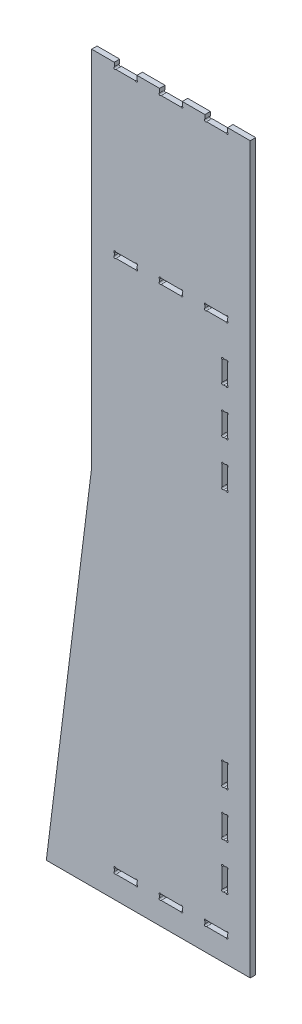
SolidWorks part; units mm, degrees
ref_plane "Front Plane" through (0, 0, 0) normal (0, 0, 1) x (1, 0, 0)
ref_plane "Top Plane" through (0, 0, 0) normal (0, 1, 0) x (1, 0, 0)
ref_plane "Right Plane" through (0, 0, 0) normal (1, 0, 0) x (0, 0, -1)
sketch "Sketch1" plane through (0, 0, 0) normal (0, 0, 1) x (1, 0, 0)
  line L0 (230.2639, 423.1047) -> (230.2639, -376.8953)
  line L1 (230.2639, -376.8953) -> (-219.7361, -376.8953)
  line L2 (-69.7361, 1218.1047) -> (-69.7361, 1214.3832)
  line L3 (-219.7361, -376.8953) -> (-119.7361, 423.1047)
  line L4 (230.2639, 423.1047) -> (230.2639, 1223.1047)
  line L5 (230.2639, 1223.1047) -> (180.2639, 1223.1047)
  line L6 (-119.7361, 1223.1047) -> (-119.7361, 423.1047)
  line L7 (-66.4577, 1211.1047) -> (-23.0146, 1211.1047)
  line L8 (-19.7361, 1214.3832) -> (-19.7361, 1218.1047)
  line L9 (-69.7361, 1223.1047) -> (-119.7361, 1223.1047)
  line L10 (30.2639, 1218.1047) -> (30.2639, 1214.3832)
  line L11 (33.5423, 1211.1047) -> (76.9854, 1211.1047)
  line L12 (80.2639, 1214.3832) -> (80.2639, 1218.1047)
  line L13 (30.2639, 1223.1047) -> (-19.7361, 1223.1047)
  line L14 (130.2639, 1218.1047) -> (130.2639, 1214.3832)
  line L15 (133.5423, 1211.1047) -> (176.9854, 1211.1047)
  line L16 (-57.4222, 1211.1047) -> (-57.4222, 862.1047) construction
  line L17 (130.2639, 1223.1047) -> (80.2639, 1223.1047)
  line L18 (-66.4574, 862.1047) -> (-23.0148, 862.1047)
  line L19 (130.2639, 1223.1047) -> (130.2639, 1218.1047)
  line L20 (80.2639, 1218.1047) -> (80.2639, 1223.1047)
  line L21 (30.2639, 1223.1047) -> (30.2639, 1218.1047)
  line L22 (-19.7361, 1218.1047) -> (-19.7361, 1223.1047)
  line L23 (-69.7361, 1223.1047) -> (-69.7361, 1218.1047)
  line L24 (33.5423, 862.1047) -> (76.9854, 862.1047)
  line L25 (-44.7361, 856.1047) -> (-19.7361, 856.1047) construction
  line L26 (-66.4574, 850.1047) -> (-23.0148, 850.1047)
  line L27 (-19.7361, 858.8267) -> (-19.7361, 853.3827)
  line L28 (155.2639, 850.1047) -> (155.2639, 862.1047) construction
  line L29 (-69.7361, 862.1047) -> (-67.3361, 862.1047) construction
  line L30 (180.2639, 1214.3832) -> (180.2639, 1223.1047)
  line L31 (155.2639, 1211.1047) -> (155.2639, 1213.3612) construction
  line L32 (130.2639, 1211.1047) -> (80.2639, 1211.1047) construction
  line L33 (105.2639, 1211.1047) -> (105.2639, 1217.0808) construction
  line L34 (30.2639, 1211.1047) -> (80.2639, 1211.1047) construction
  line L35 (80.2639, 1211.1047) -> (30.2639, 1211.1047) construction
  line L36 (55.2639, 1211.1047) -> (55.2639, 1226.1948) construction
  line L37 (30.2639, 1211.1047) -> (-19.7361, 1211.1047) construction
  line L38 (5.2639, 1211.1047) -> (5.2639, 1218.1047) construction
  line L39 (-19.7361, 1211.1047) -> (-69.7361, 1211.1047) construction
  line L40 (-44.7361, 1211.1047) -> (-44.7361, 1220.8464) construction
  line L41 (-67.3361, 862.1047) -> (-68.5361, 862.1047) construction
  line L42 (-68.5361, 862.1047) -> (-68.5361, 860.4781) construction
  line L43 (-69.7361, 862.1047) -> (-69.7361, 859.7056) construction
  line L44 (-69.7361, 859.7056) -> (-69.7361, 860.9052) construction
  line L45 (-69.7361, 860.9052) -> (-68.5361, 860.9052) construction
  line L46 (-69.7361, 858.8267) -> (-69.7361, 853.3827)
  line L47 (-44.7361, 862.1047) -> (-44.7361, 850.1047) construction
  line L48 (-44.7361, 856.1047) -> (-69.7361, 856.1047) construction
  line L49 (30.2639, 862.1047) -> (32.6639, 862.1047) construction
  line L50 (32.6639, 862.1047) -> (31.4639, 862.1047) construction
  line L51 (31.4639, 862.1047) -> (31.4639, 860.4781) construction
  line L52 (80.2639, 856.1047) -> (30.2639, 856.1047) construction
  line L53 (33.5423, 850.1047) -> (76.9854, 850.1047)
  line L54 (80.2639, 858.8262) -> (80.2639, 853.3832)
  line L55 (30.2639, 862.1047) -> (30.2639, 860.9047) construction
  line L56 (130.2639, 858.8234) -> (130.2639, 853.386)
  line L57 (133.5374, 850.1047) -> (176.9904, 850.1047)
  line L58 (180.2639, 858.8234) -> (180.2639, 853.386)
  line L59 (30.2639, 859.7047) -> (30.2639, 860.9047) construction
  line L60 (30.2639, 860.9047) -> (31.8328, 860.9047) construction
  line L61 (30.2639, 858.8262) -> (30.2639, 853.3832)
  line L62 (55.2639, 850.1047) -> (55.2639, 862.1047) construction
  line L63 (180.2639, 856.1047) -> (130.2639, 856.1047) construction
  line L64 (230.2639, -326.8953) -> (-186.18, -326.8953) construction
  line L65 (-69.7361, -314.8953) -> (-67.3361, -314.8953) construction
  line L66 (-67.3361, -314.8953) -> (-68.5361, -314.8953) construction
  line L67 (-68.5361, -314.8953) -> (-68.5361, -316.4136) construction
  line L68 (-69.7361, -314.8953) -> (-69.7361, -317.3012) construction
  line L69 (133.5374, 862.1047) -> (176.9904, 862.1047)
  line L70 (-66.4594, -326.8953) -> (-23.0129, -326.8953)
  line L71 (-69.7361, -323.6139) -> (-69.7361, -318.1767)
  line L72 (-66.4594, -314.8953) -> (-23.0129, -314.8953)
  line L73 (-19.7361, -323.6139) -> (-19.7361, -318.1767)
  line L74 (33.5423, -326.8953) -> (76.9854, -326.8953)
  line L75 (30.2639, -323.6168) -> (30.2639, -318.1738)
  line L76 (33.5423, -314.8953) -> (76.9854, -314.8953)
  line L77 (80.2639, -323.6168) -> (80.2639, -318.1738)
  line L78 (133.541, -326.8953) -> (176.9868, -326.8953)
  line L79 (130.2639, -323.6161) -> (130.2639, -318.1745)
  line L80 (155.2639, -326.8953) -> (155.2639, -314.8953) construction
  line L81 (180.2639, -323.6161) -> (180.2639, -318.1745)
  line L82 (-69.7361, -317.3012) -> (-69.7361, -316.0983) construction
  line L83 (-69.7361, -316.0983) -> (-68.0325, -316.0983) construction
  line L84 (-19.7361, -320.8953) -> (-69.7361, -320.8953) construction
  line L85 (-44.7361, -326.8953) -> (-44.7361, -314.8953) construction
  line L86 (30.2639, -314.8953) -> (32.6639, -314.8953) construction
  line L87 (32.6639, -314.8953) -> (31.4639, -314.8953) construction
  line L88 (31.4639, -314.8953) -> (31.4639, -316.5927) construction
  line L89 (30.2639, -314.8953) -> (30.2639, -317.2953) construction
  line L90 (30.2639, -317.2953) -> (30.2639, -316.0953) construction
  line L91 (30.2639, -316.0953) -> (31.9728, -316.0953) construction
  line L92 (80.2639, -320.8953) -> (30.2639, -320.8953) construction
  line L93 (55.2639, -326.8953) -> (55.2639, -314.8953) construction
  line L94 (180.2639, -320.8953) -> (130.2639, -320.8953) construction
  line L95 (168.2639, 8.1661) -> (169.4639, 8.1661) construction
  line L96 (171.5423, 8.1661) -> (176.9854, 8.1661)
  line L97 (180.2639, -16.8339) -> (168.2639, -16.8339) construction
  line L98 (171.5423, -41.8339) -> (176.9854, -41.8339)
  line L99 (180.2639, 4.8876) -> (180.2639, -38.5555)
  line L100 (133.541, -314.8953) -> (176.9868, -314.8953)
  line L101 (180.2639, -116.8339) -> (168.2639, -116.8339) construction
  line L102 (168.2639, -95.1124) -> (168.2639, -138.5555)
  line L103 (171.5423, -141.8339) -> (176.9854, -141.8339)
  line L104 (180.2639, -95.1124) -> (180.2639, -138.5555)
  line L105 (171.5423, -191.8339) -> (176.9854, -191.8339)
  line L106 (180.2639, -216.8339) -> (168.2639, -216.8339) construction
  line L107 (171.5423, -241.8339) -> (176.9854, -241.8339)
  line L108 (180.2639, -195.1124) -> (180.2639, -238.5555)
  line L109 (170.6639, 8.1661) -> (169.4639, 8.1661) construction
  line L110 (169.4639, 8.1661) -> (169.4639, 6.5299) construction
  line L111 (168.2639, 8.1661) -> (168.2639, 5.7661) construction
  line L112 (168.2639, 5.7661) -> (168.2639, 6.9661) construction
  line L113 (168.2639, 6.9661) -> (169.814, 6.9661) construction
  line L114 (168.2639, 4.8876) -> (168.2639, -38.5555)
  line L115 (174.2639, -41.8339) -> (174.2639, 8.1661) construction
  line L116 (168.2639, -91.8339) -> (170.6639, -91.8339) construction
  line L117 (170.6639, -91.8339) -> (169.4639, -91.8339) construction
  line L118 (169.4639, -91.8339) -> (169.4639, -93.6696) construction
  line L119 (168.2639, -91.8339) -> (168.2639, -94.2339) construction
  line L120 (168.2639, -94.2339) -> (168.2639, -93.0339) construction
  line L121 (168.2639, -93.0339) -> (170.0371, -93.0339) construction
  line L122 (171.5423, -91.8339) -> (176.9854, -91.8339)
  line L123 (174.2639, -141.8339) -> (174.2639, -91.8339) construction
  line L124 (168.2639, -191.8339) -> (170.6639, -191.8339) construction
  line L125 (170.6639, -191.8339) -> (169.4639, -191.8339) construction
  line L126 (169.4639, -191.8339) -> (169.4639, -193.433) construction
  line L127 (168.2639, -191.8339) -> (168.2639, -194.2339) construction
  line L128 (168.2639, -194.2339) -> (168.2639, -193.0339) construction
  line L129 (168.2639, -193.0339) -> (170.0371, -193.0339) construction
  line L130 (168.2639, -195.1124) -> (168.2639, -238.5555)
  line L131 (174.2639, -241.8339) -> (174.2639, -191.8339) construction
  line L132 (66.4354, 850.1047) -> (66.4354, -314.8953) construction
  line L133 (66.4354, -314.8953) -> (66.4354, 267.6047) construction
  line L134 (66.4354, 267.6047) -> (230.2639, 267.6047) construction
  line L135 (66.4354, 267.6047) -> (-139.1736, 267.6047) construction
  line L136 (174.2639, 777.0433) -> (174.2639, 727.0433) construction
  line L137 (168.2639, 728.2433) -> (170.0371, 728.2433) construction
  line L138 (168.2639, 729.4433) -> (168.2639, 728.2433) construction
  line L139 (168.2639, 727.0433) -> (168.2639, 729.4433) construction
  line L140 (169.4639, 727.0433) -> (169.4639, 728.6424) construction
  line L141 (170.6639, 727.0433) -> (169.4639, 727.0433) construction
  line L142 (168.2639, 727.0433) -> (170.6639, 727.0433) construction
  line L143 (174.2639, 677.0433) -> (174.2639, 627.0433) construction
  line L144 (168.2639, 628.2433) -> (170.0371, 628.2433) construction
  line L145 (168.2639, 629.4433) -> (168.2639, 628.2433) construction
  line L146 (168.2639, 627.0433) -> (168.2639, 629.4433) construction
  line L147 (169.4639, 627.0433) -> (169.4639, 628.879) construction
  line L148 (170.6639, 627.0433) -> (169.4639, 627.0433) construction
  line L149 (168.2639, 627.0433) -> (170.6639, 627.0433) construction
  line L150 (174.2639, 577.0433) -> (174.2639, 527.0433) construction
  line L151 (168.2639, 528.2433) -> (169.814, 528.2433) construction
  line L152 (168.2639, 529.4433) -> (168.2639, 528.2433) construction
  line L153 (168.2639, 527.0433) -> (168.2639, 529.4433) construction
  line L154 (169.4639, 527.0433) -> (169.4639, 528.6795) construction
  line L155 (170.6639, 527.0433) -> (169.4639, 527.0433) construction
  line L156 (180.2639, 752.0433) -> (168.2639, 752.0433) construction
  line L157 (180.2639, 652.0433) -> (168.2639, 652.0433) construction
  line L158 (180.2639, 552.0433) -> (168.2639, 552.0433) construction
  line L159 (168.2639, 527.0433) -> (169.4639, 527.0433) construction
  line L160 (168.2639, 730.3218) -> (168.2639, 773.7649)
  line L161 (171.5423, 627.0433) -> (176.9854, 627.0433)
  line L162 (168.2639, 530.3218) -> (168.2639, 573.7649)
  line L163 (180.2639, 730.3218) -> (180.2639, 773.7649)
  line L164 (171.5423, 777.0433) -> (176.9854, 777.0433)
  line L165 (171.5423, 727.0433) -> (176.9854, 727.0433)
  line L166 (180.2639, 630.3218) -> (180.2639, 673.7649)
  line L167 (171.5423, 677.0433) -> (176.9854, 677.0433)
  line L168 (168.2639, 630.3218) -> (168.2639, 673.7649)
  line L169 (180.2639, 530.3218) -> (180.2639, 573.7649)
  line L170 (171.5423, 577.0433) -> (176.9854, 577.0433)
  line L171 (171.5423, 527.0433) -> (176.9854, 527.0433)
  circle A0 centre (-69.7361, 862.1047) radius 2.4 construction
  arc A1 (176.9854, 1211.1047) -> (180.2639, 1214.3832) centre (179.0639, 1212.3047) ccw
  arc A2 (133.5423, 1211.1047) -> (130.2639, 1214.3832) centre (131.4639, 1212.3047) cw
  arc A3 (76.9854, 1211.1047) -> (80.2639, 1214.3832) centre (79.0639, 1212.3047) ccw
  arc A4 (33.5423, 1211.1047) -> (30.2639, 1214.3832) centre (31.4639, 1212.3047) cw
  arc A5 (-23.0146, 1211.1047) -> (-19.7361, 1214.3832) centre (-20.9361, 1212.3047) ccw
  arc A6 (-66.4577, 1211.1047) -> (-69.7361, 1214.3832) centre (-68.5361, 1212.3047) cw
  arc A7 (-66.4574, 862.1047) -> (-69.7361, 858.8267) centre (-68.5361, 860.9052) ccw
  arc A8 (-23.0148, 862.1047) -> (-19.7361, 858.8267) centre (-20.9361, 860.9052) cw
  arc A9 (-23.0148, 850.1047) -> (-19.7361, 853.3827) centre (-20.9361, 851.3042) ccw
  arc A10 (-66.4574, 850.1047) -> (-69.7361, 853.3827) centre (-68.5361, 851.3042) cw
  circle A11 centre (30.2639, 862.1047) radius 2.4 construction
  arc A12 (33.5423, 862.1047) -> (30.2639, 858.8262) centre (31.4639, 860.9047) ccw
  arc A13 (76.9854, 862.1047) -> (80.2639, 858.8262) centre (79.0639, 860.9047) cw
  arc A14 (76.9854, 850.1047) -> (80.2639, 853.3832) centre (79.0639, 851.3047) ccw
  arc A15 (33.5423, 850.1047) -> (30.2639, 853.3832) centre (31.4639, 851.3047) cw
  arc A16 (176.9904, 862.1047) -> (180.2639, 858.8234) centre (179.0688, 860.9047) cw
  arc A17 (133.5374, 862.1047) -> (130.2639, 858.8234) centre (131.4589, 860.9047) ccw
  arc A18 (176.9904, 850.1047) -> (180.2639, 853.386) centre (179.0688, 851.3047) ccw
  arc A19 (133.5374, 850.1047) -> (130.2639, 853.386) centre (131.4589, 851.3047) cw
  circle A20 centre (-69.7361, -314.8953) radius 2.4 construction
  arc A21 (-66.4594, -314.8953) -> (-69.7361, -318.1767) centre (-68.5361, -316.0983) ccw
  arc A22 (-23.0129, -314.8953) -> (-19.7361, -318.1767) centre (-20.9361, -316.0983) cw
  arc A23 (-23.0129, -326.8953) -> (-19.7361, -323.6139) centre (-20.9361, -325.6923) ccw
  arc A24 (-66.4594, -326.8953) -> (-69.7361, -323.6139) centre (-68.5361, -325.6923) cw
  circle A25 centre (30.2639, -314.8953) radius 2.4 construction
  arc A26 (33.5423, -314.8953) -> (30.2639, -318.1738) centre (31.4639, -316.0953) ccw
  arc A27 (76.9854, -314.8953) -> (80.2639, -318.1738) centre (79.0639, -316.0953) cw
  arc A28 (76.9854, -326.8953) -> (80.2639, -323.6168) centre (79.0639, -325.6953) ccw
  arc A29 (33.5423, -326.8953) -> (30.2639, -323.6168) centre (31.4639, -325.6953) cw
  arc A30 (176.9868, -314.8953) -> (180.2639, -318.1745) centre (179.0652, -316.0953) cw
  arc A31 (133.541, -314.8953) -> (130.2639, -318.1745) centre (131.4625, -316.0953) ccw
  arc A32 (176.9868, -326.8953) -> (180.2639, -323.6161) centre (179.0652, -325.6953) ccw
  arc A33 (133.541, -326.8953) -> (130.2639, -323.6161) centre (131.4625, -325.6953) cw
  circle A34 centre (168.2639, 8.1661) radius 2.4 construction
  arc A35 (171.5423, 8.1661) -> (168.2639, 4.8876) centre (169.4639, 6.9661) ccw
  arc A36 (176.9854, 8.1661) -> (180.2639, 4.8876) centre (179.0639, 6.9661) cw
  arc A37 (176.9854, -41.8339) -> (180.2639, -38.5555) centre (179.0639, -40.6339) ccw
  arc A38 (171.5423, -41.8339) -> (168.2639, -38.5555) centre (169.4639, -40.6339) cw
  circle A39 centre (168.2639, -91.8339) radius 2.4 construction
  arc A40 (171.5423, -91.8339) -> (168.2639, -95.1124) centre (169.4639, -93.0339) ccw
  arc A41 (176.9854, -91.8339) -> (180.2639, -95.1124) centre (179.0639, -93.0339) cw
  arc A42 (176.9854, -141.8339) -> (180.2639, -138.5555) centre (179.0639, -140.6339) ccw
  arc A43 (171.5423, -141.8339) -> (168.2639, -138.5555) centre (169.4639, -140.6339) cw
  circle A44 centre (168.2639, -191.8339) radius 2.4 construction
  arc A45 (171.5423, -191.8339) -> (168.2639, -195.1124) centre (169.4639, -193.0339) ccw
  arc A46 (176.9854, -191.8339) -> (180.2639, -195.1124) centre (179.0639, -193.0339) cw
  arc A47 (176.9854, -241.8339) -> (180.2639, -238.5555) centre (179.0639, -240.6339) ccw
  arc A48 (171.5423, -241.8339) -> (168.2639, -238.5555) centre (169.4639, -240.6339) cw
  circle A49 centre (168.2639, 727.0433) radius 2.4 construction
  circle A50 centre (168.2639, 627.0433) radius 2.4 construction
  circle A51 centre (168.2639, 527.0433) radius 2.4 construction
  arc A52 (171.5423, 777.0433) -> (168.2639, 773.7649) centre (169.4639, 775.8433) ccw
  arc A53 (176.9854, 777.0433) -> (180.2639, 773.7649) centre (179.0639, 775.8433) cw
  arc A54 (176.9854, 727.0433) -> (180.2639, 730.3218) centre (179.0639, 728.2433) ccw
  arc A55 (171.5423, 727.0433) -> (168.2639, 730.3218) centre (169.4639, 728.2433) cw
  arc A56 (171.5423, 677.0433) -> (168.2639, 673.7649) centre (169.4639, 675.8433) ccw
  arc A57 (176.9854, 677.0433) -> (180.2639, 673.7649) centre (179.0639, 675.8433) cw
  arc A58 (176.9854, 627.0433) -> (180.2639, 630.3218) centre (179.0639, 628.2433) ccw
  arc A59 (171.5423, 627.0433) -> (168.2639, 630.3218) centre (169.4639, 628.2433) cw
  arc A60 (171.5423, 577.0433) -> (168.2639, 573.7649) centre (169.4639, 575.8433) ccw
  arc A61 (176.9854, 577.0433) -> (180.2639, 573.7649) centre (179.0639, 575.8433) cw
  arc A62 (176.9854, 527.0433) -> (180.2639, 530.3218) centre (179.0639, 528.2433) ccw
  arc A63 (171.5423, 527.0433) -> (168.2639, 530.3218) centre (169.4639, 528.2433) cw
  point P2 (-69.7361, 1223.1047)
  point P8 (30.2639, 1223.1047)
  point P10 (-19.7361, 1223.1047)
  point P12 (80.2639, 1223.1047)
  point P14 (130.2639, 1223.1047)
  dimension "D26" = 4.8
  dimension "D15" = 50
  dimension "D27" = 4.8
  dimension "D8" = 4.8
  dimension "D19" = 4.8
  dimension "D13" = 50
  dimension "D21" = 4.8
  dimension "D32" = 4.8
  dimension "D33" = 4.8
  dimension "D14" = 4.8
  dimension "D28" = 4.8
  dimension "D31" = 4.8
  dimension "D41" = 4.8
  dimension "D42" = 4.8
  dimension "D30" = 4.8
  dimension "D34" = 4.8
  dimension "D35" = 4.8
  dimension "D36" = 4.8
  dimension "D1" = 800
  dimension "D2" = 450
  dimension "D3" = 350
  dimension "D4" = 800
  dimension "D5" = 350
  dimension "D6" = 50
  dimension "D7" = 50
  dimension "D9" = 50
  dimension "D10" = 50
  dimension "D11" = 12
  dimension "D12" = 50
  dimension "D16" = 5
  dimension "D17" = 349
  dimension "D18" = 5
  dimension "D20" = 5
  dimension "D22" = 5
  dimension "D23" = 0
  dimension "D24" = 5
  dimension "D25" = 0
  dimension "D29" = 50
  dimension "D39" = 50
extrude "Boss-Extrude1" add sketch "Sketch1" along normal blind 12
